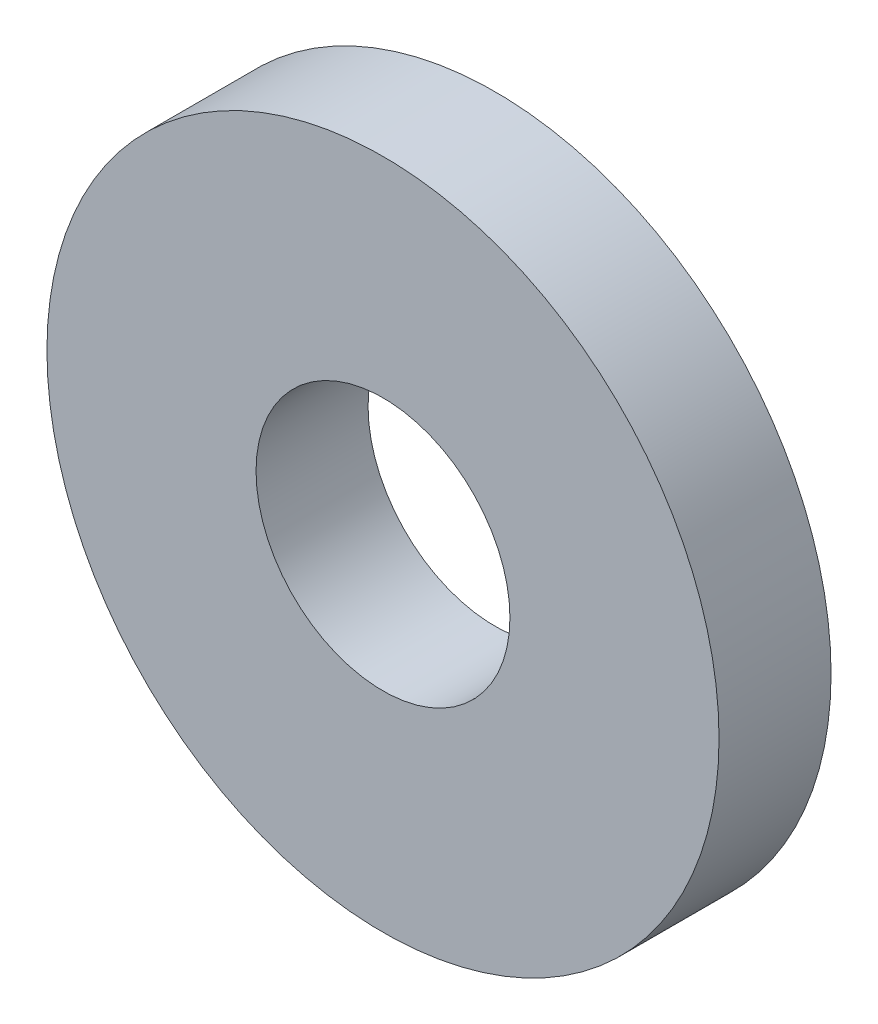
SolidWorks part; units mm, degrees
ref_plane "Ebene vorne" through (0, 0, 0) normal (0, 0, 1) x (1, 0, 0)
ref_plane "Ebene oben" through (0, 0, 0) normal (0, 1, 0) x (1, 0, 0)
ref_plane "Ebene rechts" through (0, 0, 0) normal (1, 0, 0) x (0, 0, -1)
sketch "Skizze1" plane through (0, 0, 0) normal (0, 0, 1) x (1, 0, 0)
  circle A0 centre (0, 0) radius 17
  circle A1 centre (0, 0) radius 45
  dimension "D1" = 34
  dimension "D2" = 90
extrude "Aufsatz-Linear austragen1" add sketch "Skizze1" against normal blind 15
